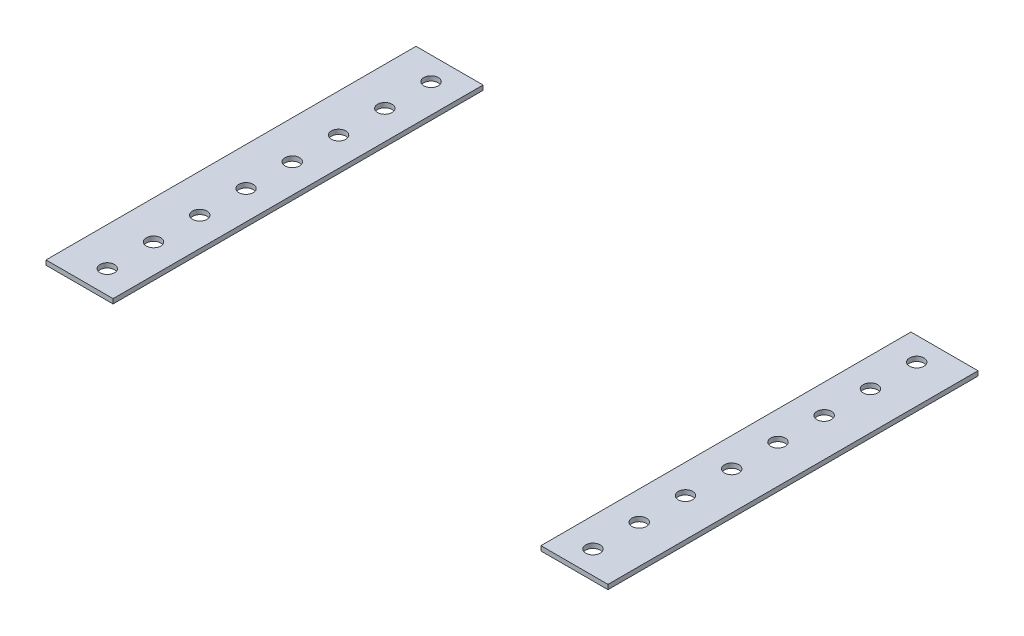
SolidWorks part; units mm, degrees
ref_plane "Front Plane" through (0, 0, 0) normal (0, 0, 1) x (1, 0, 0)
ref_plane "Top Plane" through (0, 0, 0) normal (0, 1, 0) x (1, 0, 0)
ref_plane "Right Plane" through (0, 0, 0) normal (1, 0, 0) x (0, 0, -1)
sketch "Sketch1" plane through (0, 0, 0) normal (0, 1, 0) x (1, 0, 0)
  line L0 (16.1699, 175.4998) -> (16.1699, -258.7183) construction
  line L1 (-138.1351, 175.4998) -> (170.4749, 175.4998) construction
  line L2 (-138.1351, 175.4998) -> (-138.1351, -258.7183) construction
  line L3 (-138.1351, -258.7183) -> (170.4749, -258.7183) construction
  line L4 (170.4749, 175.4998) -> (170.4749, -258.7183) construction
  line L5 (-138.1351, 175.4998) -> (-101.3051, 175.4998)
  line L6 (-138.1351, 175.4998) -> (-138.1351, -27.7002)
  line L7 (-138.1351, -27.7002) -> (-101.3051, -27.7002)
  line L8 (-101.3051, 175.4998) -> (-101.3051, -27.7002)
  line L9 (170.4749, -27.7002) -> (133.6449, -27.7002)
  line L10 (170.4749, 175.4998) -> (133.6449, 175.4998)
  line L11 (170.4749, 175.4998) -> (170.4749, -27.7002)
  line L12 (133.6449, 175.4998) -> (133.6449, -27.7002)
  dimension "D1" = 308.61
  dimension "D2" = 203.2
  dimension "D3" = 36.83
extrude "Boss-Extrude1" add sketch "Sketch1" against normal blind 2.54
sketch "Sketch2" plane through (0, 0, 0) normal (0, 1, 0) x (1, 0, 0)
  line L0 (-138.1351, 175.4998) -> (-138.1351, -27.7002) construction
  line L1 (-138.1351, -27.7002) -> (-101.3051, -27.7002) construction
  line L2 (-101.3051, -27.7002) -> (-101.3051, 175.4998) construction
  line L3 (-101.3051, 175.4998) -> (-138.1351, 175.4998) construction
  line L4 (-117.1801, 175.4998) -> (-117.1801, -27.7002) construction
  line L5 (-138.1351, 175.4998) -> (170.4749, 175.4998) construction
  line L6 (16.1699, 175.4998) -> (16.1699, -27.7002) construction
  line L7 (-138.1351, -27.7002) -> (170.4749, -27.7002) construction
  line L8 (149.5199, 175.4998) -> (149.5199, -27.7002) construction
  line L9 (133.6449, 175.4998) -> (170.4749, 175.4998) construction
  line L10 (133.6449, -27.7002) -> (133.6449, 175.4998) construction
  line L11 (170.4749, -27.7002) -> (133.6449, -27.7002) construction
  line L12 (170.4749, 175.4998) -> (170.4749, -27.7002) construction
  circle A1 centre (-117.1801, 162.7998) radius 3.9687
  circle A2 centre (-117.1801, 137.3998) radius 3.9687
  circle A3 centre (-117.1801, 111.9998) radius 3.9687
  circle A4 centre (-117.1801, 86.5998) radius 3.9688
  circle A5 centre (-117.1801, 61.1998) radius 3.9688
  circle A6 centre (-117.1801, 35.7998) radius 3.9688
  circle A7 centre (-117.1801, 10.3998) radius 3.9687
  circle A8 centre (-117.1801, -15.0002) radius 3.9687
  circle A9 centre (149.5199, -15.0002) radius 3.9687
  circle A10 centre (149.5199, 10.3998) radius 3.9687
  circle A11 centre (149.5199, 35.7998) radius 3.9688
  circle A12 centre (149.5199, 61.1998) radius 3.9688
  circle A13 centre (149.5199, 86.5998) radius 3.9688
  circle A14 centre (149.5199, 111.9998) radius 3.9687
  circle A15 centre (149.5199, 137.3998) radius 3.9687
  circle A16 centre (149.5199, 162.7998) radius 3.9687
  dimension "D2" = 7.9375
  dimension "D11" = 7.9375
  dimension "D12" = 7.9375
  dimension "D13" = 7.9375
  dimension "D14" = 7.9375
  dimension "D15" = 7.9375
  dimension "D16" = 7.9375
  dimension "D17" = 7.9375
  dimension "D1" = 15.875
  dimension "D3" = 12.7
  dimension "D4" = 25.4
  dimension "D5" = 25.4
  dimension "D6" = 25.4
  dimension "D7" = 25.4
  dimension "D8" = 25.4
  dimension "D9" = 25.4
  dimension "D10" = 25.4
extrude "Cut-Extrude1" cut sketch "Sketch2" against normal up to next (2.54 mm away)
